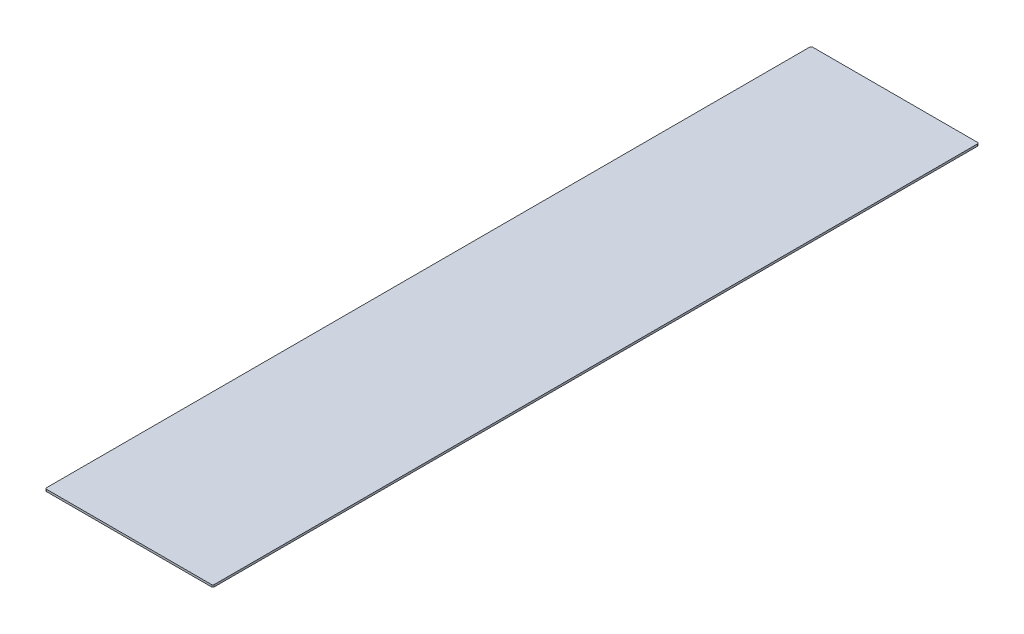
SolidWorks part; units mm, degrees
ref_plane "Front Plane" through (0, 0, 0) normal (0, 0, 1) x (1, 0, 0)
ref_plane "Top Plane" through (0, 0, 0) normal (0, 1, 0) x (1, 0, 0)
ref_plane "Right Plane" through (0, 0, 0) normal (1, 0, 0) x (0, 0, -1)
sketch "Sketch2" plane through (0, 0, 0) normal (0, 1, 0) x (1, 0, 0)
  line L1 (-118.75, -551.5) -> (118.75, -551.5)
  line L2 (-120.75, -549.5) -> (-120.75, 549.5)
  line L3 (-118.75, 551.5) -> (118.75, 551.5)
  line L4 (120.75, -549.5) -> (120.75, 549.5)
  line L5 (-120.75, -551.5) -> (120.75, 551.5) construction
  line L6 (-120.75, 551.5) -> (120.75, -551.5) construction
  arc A0 (-120.75, 549.5) -> (-118.75, 551.5) centre (-118.75, 549.5) cw
  arc A1 (-118.75, -551.5) -> (-120.75, -549.5) centre (-118.75, -549.5) cw
  arc A2 (118.75, -551.5) -> (120.75, -549.5) centre (118.75, -549.5) ccw
  arc A3 (118.75, 551.5) -> (120.75, 549.5) centre (118.75, 549.5) cw
  point P0 (0, 0)
  dimension "D3" = 2
  dimension "D1" = 241.5
  dimension "D2" = 1103
extrude "Boss-Extrude1" add sketch "Sketch2" along normal blind 3
